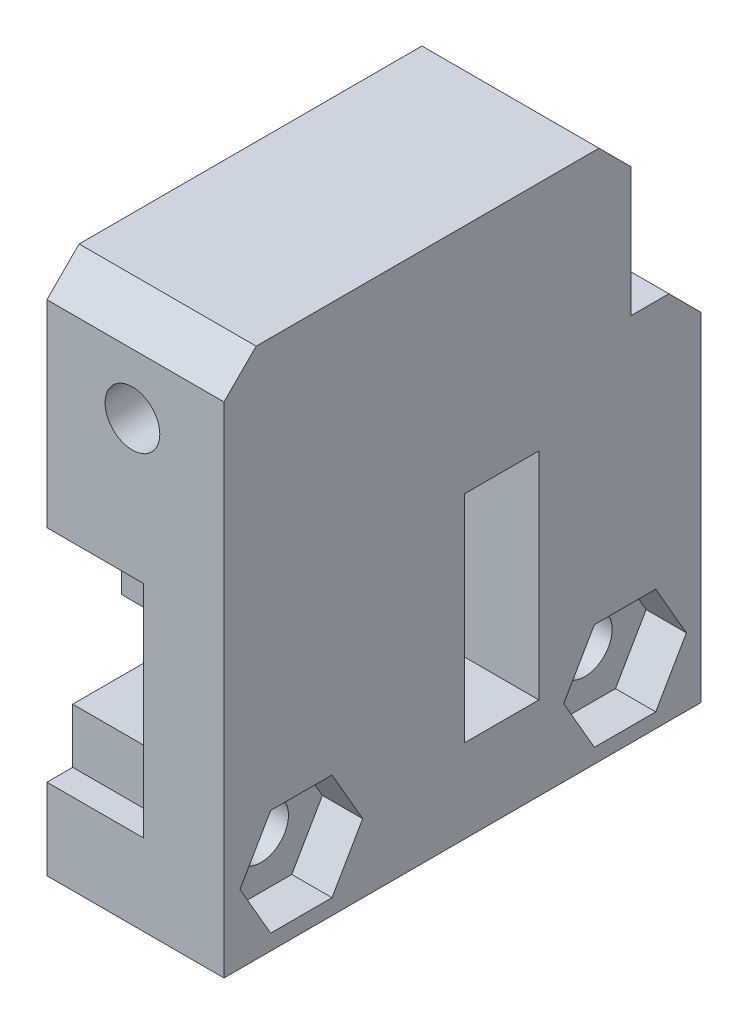
SolidWorks part; units mm, degrees
ref_plane "Front Plane" through (0, 0, 0) normal (0, 0, 1) x (1, 0, 0)
ref_plane "Top Plane" through (0, 0, 0) normal (0, 1, 0) x (1, 0, 0)
ref_plane "Right Plane" through (0, 0, 0) normal (1, 0, 0) x (0, 0, -1)
sketch "Sketch1" plane through (0, 0, 0) normal (1, 0, 0) x (0, 0, -1)
  line L1 (-14.8204, 11.4976) -> (14.8204, 11.4976)
  line L2 (-14.8204, 11.4976) -> (-14.8204, -11.4976)
  line L3 (-14.8204, -11.4976) -> (14.8204, -11.4976)
  line L4 (14.8204, 11.4976) -> (14.8204, -11.4976)
  line L5 (-14.8204, 11.4976) -> (14.8204, -11.4976) construction
  line L6 (-14.8204, -11.4976) -> (14.8204, 11.4976) construction
  point P0 (0, 0)
extrude "Boss-Extrude1" add sketch "Sketch1" along normal blind 11
sketch "Sketch2" plane through (0, 11.4976, 0) normal (0, 1, 0) x (1, 0, 0)
  line L0 (11, 14.8204) -> (11, -14.8204) construction
  line L1 (0, -14.8204) -> (11, -14.8204)
  line L2 (0, -14.8204) -> (0, 10.4797)
  line L3 (0, 10.4797) -> (11, 10.4797)
  line L4 (11, -14.8204) -> (11, 10.4797)
  line L5 (0, -14.8204) -> (11, 10.4797) construction
  line L6 (0, 10.4797) -> (11, -14.8204) construction
  point P0 (5.5, -2.1704)
extrude "Boss-Extrude2" add sketch "Sketch2" along normal blind 10
chamfer "Chamfer1" distance 2 angle 45 3 edges at (5.5, 11.4976, -14.8204) (5.5, 21.4976, -10.4797) (5.5, 21.4976, 14.8204)
sketch "Sketch3" plane through (0, 0, 0) normal (-1, 0, 0) x (0, 0, 1)
  line L1 (-15.4578, 7.2288) -> (15.9867, 7.2288)
  line L2 (-15.4578, 7.2288) -> (-15.4578, -6.4617)
  line L3 (-15.4578, -6.4617) -> (15.9867, -6.4617)
  line L4 (15.9867, 7.2288) -> (15.9867, -6.4617)
  line L5 (-15.4578, 7.2288) -> (15.9867, -6.4617) construction
  line L6 (-15.4578, -6.4617) -> (15.9867, 7.2288) construction
  point P0 (0.2645, 0.3836)
extrude "Cut-Extrude2" cut sketch "Sketch3" against normal blind 6
sketch "Sketch4" plane through (6, 0.4351, 0) normal (-1, 0, 0) x (0, 0, 1)
  line L1 (-10.6052, 3.1028) -> (6.196, 3.1028)
  line L2 (-10.6052, 3.1028) -> (-10.6052, -3.1074)
  line L3 (-10.6052, -3.1074) -> (6.196, -3.1074)
  line L4 (6.196, 3.1028) -> (6.196, -3.1074)
  line L5 (-10.6052, 3.1028) -> (6.196, -3.1074) construction
  line L6 (-10.6052, -3.1074) -> (6.196, 3.1028) construction
  point P0 (-2.2046, -0.0023)
extrude "Boss-Extrude3" add sketch "Sketch4" along normal blind 10
sketch "Sketch5" plane through (0, 0, 6.196) normal (0, 0, 1) x (1, 0, 0)
  circle A0 centre (0.2128, 0.3697) radius 2.041
extrude "Cut-Extrude3" cut sketch "Sketch5" against normal through all contours A0
sketch "Sketch6" plane through (11, 0, 0) normal (1, 0, 0) x (0, 0, -1)
  line L1 (4.7403, 7.0824) -> (0.1188, 7.0824)
  line L2 (4.7403, 7.0824) -> (4.7403, -6.3163)
  line L3 (4.7403, -6.3163) -> (0.1188, -6.3163)
  line L4 (0.1188, 7.0824) -> (0.1188, -6.3163)
  line L5 (4.7403, 7.0824) -> (0.1188, -6.3163) construction
  line L6 (4.7403, -6.3163) -> (0.1188, 7.0824) construction
  point P0 (2.4296, 0.3831)
extrude "Cut-Extrude4" cut sketch "Sketch6" against normal through all contours L4 L3 L2 L1
sketch "Sketch7" plane through (0, 0, 14.8204) normal (0, 0, 1) x (1, 0, 0)
  circle A0 centre (5.3121, 15.7624) radius 1.7
extrude "Cut-Extrude5" cut sketch "Sketch7" against normal blind 27 contours A0
sketch "Sketch15" plane through (11, 0, 0) normal (1, 0, 0) x (0, 0, -1)
  line L1 (-8.1098, -10.532) -> (-6.2046, -7.232)
  line L2 (-6.2046, -7.232) -> (-8.1098, -3.932)
  line L3 (-8.1098, -3.932) -> (-11.9203, -3.932)
  line L4 (-11.9203, -3.932) -> (-13.8256, -7.232)
  line L5 (-13.8256, -7.232) -> (-11.9203, -10.532)
  line L6 (-11.9203, -10.532) -> (-8.1098, -10.532)
  circle A0 centre (-10.0151, -7.232) radius 3.3 construction
sketch "Sketch17" plane through (11, 0, 0) normal (1, 0, 0) x (0, 0, -1)
  line L1 (12.0026, -10.5904) -> (13.9079, -7.2904)
  line L2 (13.9079, -7.2904) -> (12.0026, -3.9904)
  line L3 (12.0026, -3.9904) -> (8.1921, -3.9904)
  line L4 (8.1921, -3.9904) -> (6.2869, -7.2904)
  line L5 (6.2869, -7.2904) -> (8.1921, -10.5904)
  line L6 (8.1921, -10.5904) -> (12.0026, -10.5904)
  circle A0 centre (10.0974, -7.2904) radius 3.3 construction
sketch "Sketch18" plane through (11, 0, 0) normal (1, 0, 0) x (0, 0, -1)
  circle A0 centre (10.0974, -7.2904) radius 1.7
sketch "Sketch19" plane through (11, 0, 0) normal (1, 0, 0) x (0, 0, -1)
  circle A0 centre (-10.0151, -7.232) radius 1.7
sketch "Sketch20" plane through (11, 0, 0) normal (1, 0, 0) x (0, 0, -1)
  line L1 (-13.2201, -3.0643) -> (-6.81, -3.0643)
  line L2 (-13.2201, -3.0643) -> (-13.2201, -11.3998)
  line L3 (-13.2201, -11.3998) -> (-6.81, -11.3998)
  line L4 (-6.81, -3.0643) -> (-6.81, -11.3998)
  line L5 (-13.2201, -3.0643) -> (-6.81, -11.3998) construction
  line L6 (-13.2201, -11.3998) -> (-6.81, -3.0643) construction
  point P0 (-10.0151, -7.232)
sketch "Sketch21" plane through (11, 0, 0) normal (1, 0, 0) x (0, 0, -1)
  line L1 (6.8923, -3.1226) -> (13.3024, -3.1226)
  line L2 (6.8923, -3.1226) -> (6.8923, -11.4581)
  line L3 (6.8923, -11.4581) -> (13.3024, -11.4581)
  line L4 (13.3024, -3.1226) -> (13.3024, -11.4581)
  line L5 (6.8923, -3.1226) -> (13.3024, -11.4581) construction
  line L6 (6.8923, -11.4581) -> (13.3024, -3.1226) construction
  point P0 (10.0974, -7.2904)
extrude "Boss-Extrude4" add sketch "Sketch21" against normal blind 11
extrude "Boss-Extrude5" add sketch "Sketch20" against normal blind 11
extrude "Cut-Extrude6" cut sketch "Sketch15" against normal blind 2.5
extrude "Cut-Extrude7" cut sketch "Sketch19" against normal through all
extrude "Cut-Extrude8" cut sketch "Sketch17" against normal blind 2.5
extrude "Cut-Extrude9" cut sketch "Sketch18" against normal through all
